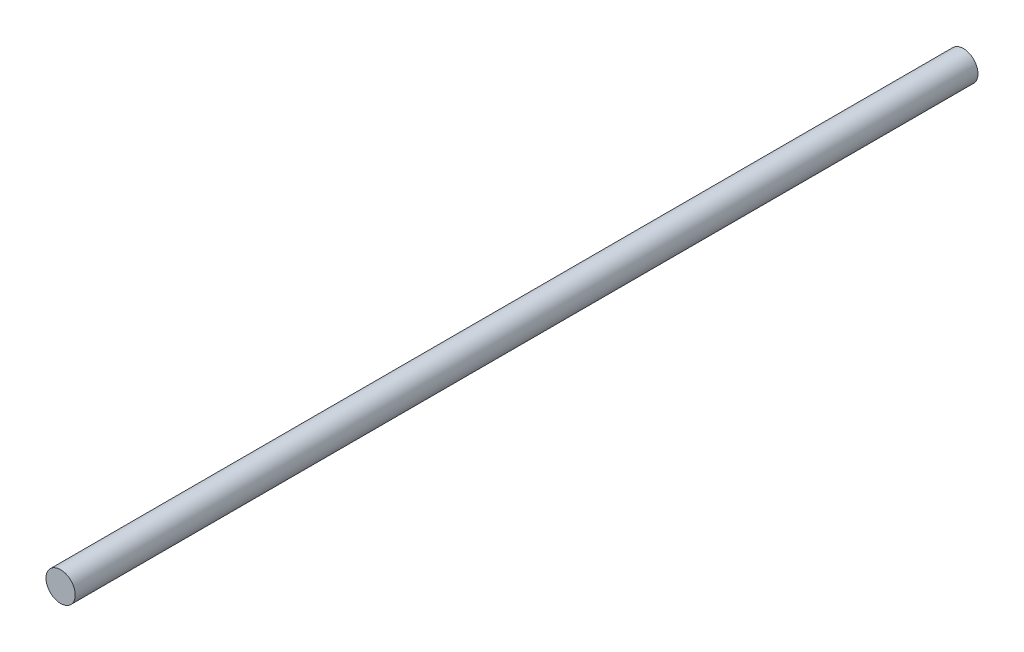
SolidWorks part; units mm, degrees
ref_plane "Front Plane" through (0, 0, 0) normal (0, 0, 1) x (1, 0, 0)
ref_plane "Top Plane" through (0, 0, 0) normal (0, 1, 0) x (1, 0, 0)
ref_plane "Right Plane" through (0, 0, 0) normal (1, 0, 0) x (0, 0, -1)
sketch "Sketch1" plane through (0, 0, 0) normal (0, 0, 1) x (1, 0, 0)
  circle A0 centre (0, 0) radius 3
  dimension "D1" = 6
extrude "Boss-Extrude1" add sketch "Sketch1" along normal blind 185
